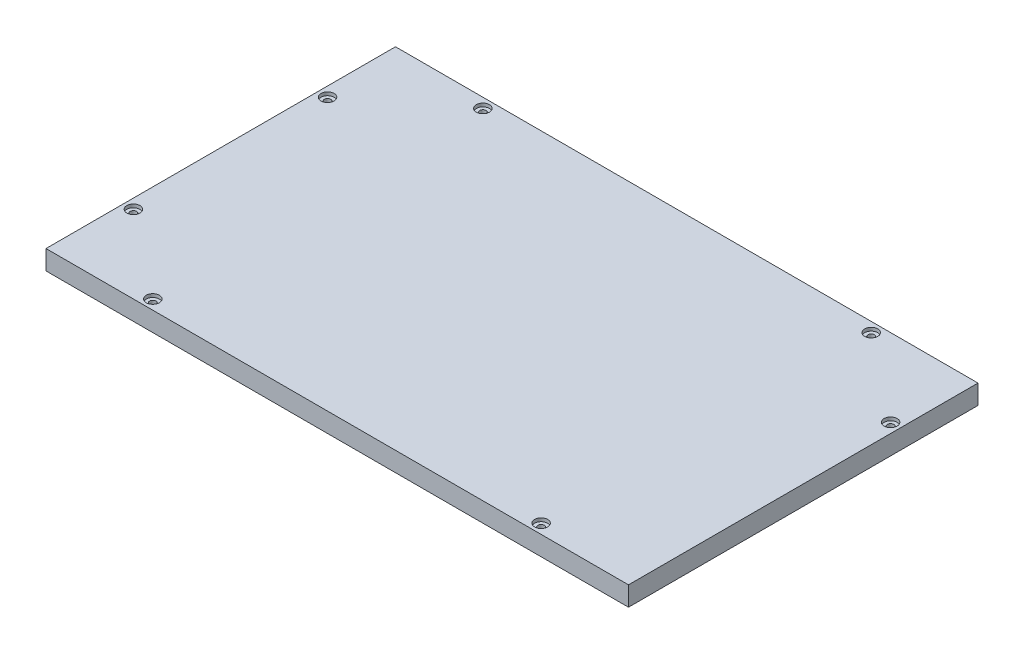
SolidWorks part; units mm, degrees
ref_plane "Front Plane" through (0, 0, 0) normal (0, 0, 1) x (1, 0, 0)
ref_plane "Top Plane" through (0, 0, 0) normal (0, 1, 0) x (1, 0, 0)
ref_plane "Right Plane" through (0, 0, 0) normal (1, 0, 0) x (0, 0, -1)
sketch "Sketch1" plane through (0, 0, 0) normal (0, 1, 0) x (1, 0, 0)
  line L1 (-128.3607, 77.7049) -> (171.6393, 77.7049)
  line L2 (-128.3607, 77.7049) -> (-128.3607, -102.2951)
  line L3 (-128.3607, -102.2951) -> (171.6393, -102.2951)
  line L4 (171.6393, 77.7049) -> (171.6393, -102.2951)
  dimension "D1" = 180
  dimension "D2" = 300
extrude "Boss-Extrude1" add sketch "Sketch1" along normal blind 10
sketch "Sketch2" plane through (0, 10, 0) normal (0, 1, 0) x (1, 0, 0)
  line L0 (-128.3607, 77.7049) -> (-128.3607, -102.2951) construction
  line L1 (-123.3607, 72.7049) -> (166.6393, 72.7049)
  line L2 (-123.3607, 72.7049) -> (-123.3607, -97.2951)
  line L3 (-123.3607, -97.2951) -> (166.6393, -97.2951)
  line L4 (166.6393, 72.7049) -> (166.6393, -97.2951)
  line L5 (171.6393, -102.2951) -> (171.6393, 77.7049) construction
  line L6 (171.6393, 77.7049) -> (-128.3607, 77.7049) construction
  line L7 (-128.3607, -102.2951) -> (171.6393, -102.2951) construction
  line L8 (-123.3607, -12.2951) -> (166.6393, -12.2951)
  line L9 (21.6393, 72.7049) -> (21.6393, -97.2951)
  point P14 (166.6393, 37.7049)
  point P15 (121.6393, 72.7049)
  point P16 (21.6393, 72.7049)
  point P19 (0, 0)
  point P20 (-78.3607, 72.7049)
  point P21 (-123.3607, 37.7049)
  point P22 (0, 0)
  point P23 (-123.3607, -62.2951)
  point P24 (121.6393, -97.2951)
  point P25 (-78.3607, -97.2951)
  point P26 (0, 0)
  point P27 (0, 0)
  point P28 (0, 0)
  dimension "D1" = 5
  dimension "D2" = 5
  dimension "D3" = 5
  dimension "D4" = 5
  dimension "D5" = 50
  dimension "D6" = 100
hole_wizard "CBORE for #4 Binding Head Machine Screw1" positions "Sketch3" profile "Sketch4" counterbore size "#4" standard "ANSI Inch" end condition up to next
sketch "Sketch3" plane through (0, 10, 0) normal (0, 1, 0) x (1, 0, 0)
  point P0 (-123.3607, 37.7049)
  point P3 (-123.3607, -62.2951)
  point P6 (-78.3607, -97.2951)
  point P9 (121.6393, -97.2951)
  point P12 (121.6393, 72.7049)
  point P15 (166.6393, 37.7049)
  point P18 (-78.3607, 72.7049)
sketch "Sketch4" plane through (-123.3607, 10, -37.7049) normal (1, 0, 0) x (0, 0, 1)
  line L0 (0, 0) -> (0, 10)
  line L1 (0, 10) -> (1.6319, 10)
  line L3 (1.6319, 10) -> (1.6319, 1.7272)
  line L4 (1.6319, 1.7272) -> (3.3731, 1.7272)
  line L5 (3.3731, 1.7272) -> (3.3731, 0)
  line L7 (3.3731, 0) -> (0, 0)
  line L11 (0, -6.35) -> (0, 107.95) construction
  dimension "Thru Hole Dia." = 3.2639
  dimension "Thru Hole Depth" = 10
  dimension "C'Bore Dia." = 6.7462
  dimension "C'Bore Depth" = 1.7272
